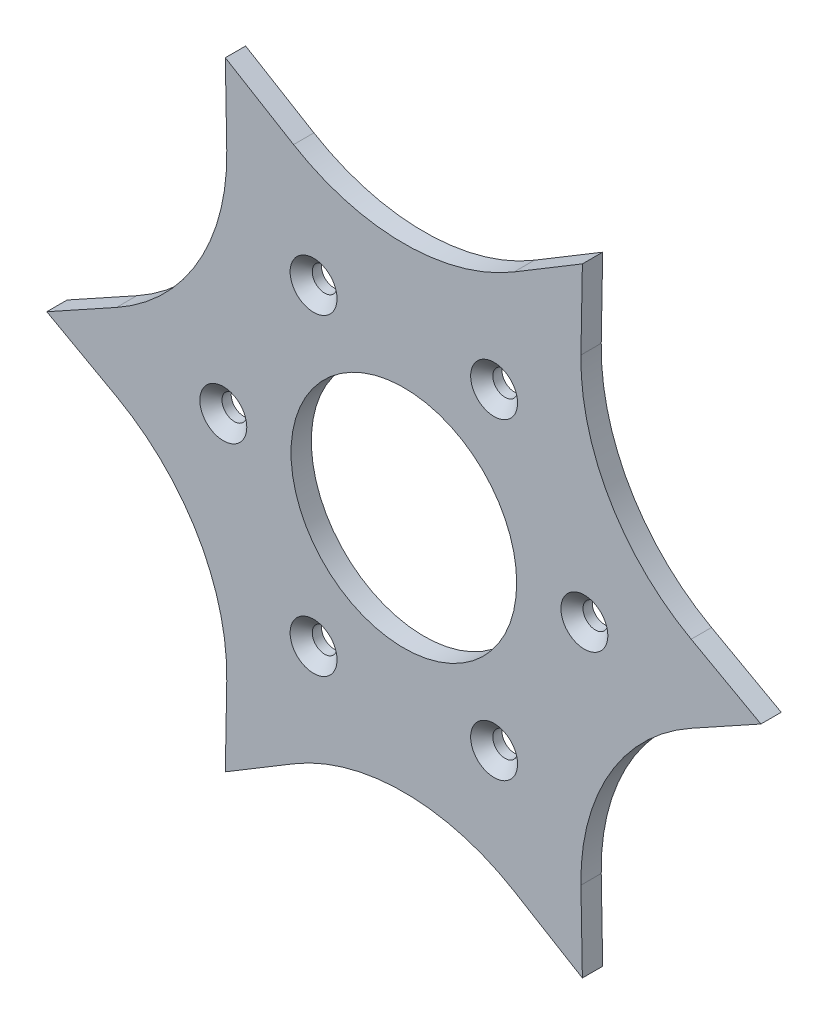
SolidWorks part; units mm, degrees
ref_plane "Front Plane" through (0, 0, 0) normal (0, 0, 1) x (1, 0, 0)
ref_plane "Top Plane" through (0, 0, 0) normal (0, 1, 0) x (1, 0, 0)
ref_plane "Right Plane" through (0, 0, 0) normal (1, 0, 0) x (0, 0, -1)
ref_plane "Plane1" through (0, 0, 62.5456) normal (0, 0, 1) x (1, 0, 0)
sketch "Sketch7" plane through (0, 0, 62.5456) normal (0, 0, 1) x (1, 0, 0)
  line L60 (-39.5574, -68.5154) -> (-24.4318, -59.4109)
  line L63 (39.5574, -68.5154) -> (24.4318, -59.4109)
  line L65 (-39.5574, -68.5154) -> (-39.2354, -50.864)
  line L66 (-79.1148, 0) -> (-63.6672, -8.5469)
  line L69 (-79.1148, 0) -> (-63.6672, 8.5469)
  line L70 (-39.5574, 68.5154) -> (-39.2354, 50.864)
  line L73 (-39.5574, 68.5154) -> (-24.4318, 59.4109)
  line L74 (39.5574, 68.5154) -> (24.4318, 59.4109)
  line L77 (39.5574, 68.5154) -> (39.2354, 50.864)
  line L78 (79.1148, 0) -> (63.6672, 8.5469)
  line L81 (79.1148, 0) -> (63.6672, -8.5469)
  line L82 (39.5574, -68.5154) -> (39.2354, -50.864)
  circle A1 centre (0, 0) radius 25
  circle A19 centre (0, 0) radius 47.9176 construction
  arc A32 (24.4318, -59.4109) -> (-24.4318, -59.4109) centre (0, -100) ccw
  arc A35 (-39.2354, -50.864) -> (-63.6672, -8.5469) centre (-86.6025, -50) ccw
  arc A37 (-63.6672, 8.5469) -> (-39.2354, 50.864) centre (-86.6025, 50) ccw
  arc A39 (-24.4318, 59.4109) -> (24.4318, 59.4109) centre (0, 100) ccw
  arc A41 (39.2354, 50.864) -> (63.6672, 8.5469) centre (86.6025, 50) ccw
  arc A43 (63.6672, -8.5469) -> (39.2354, -50.864) centre (86.6025, -50) ccw
  point P32 (0, 0)
  point P39 (-85.1007, 50.0037)
  point P40 (46.5, 100)
  point P41 (0, 100)
  point P42 (-41.6025, 50)
  point P43 (-40.1025, 50)
  point P45 (-86.6025, 50)
  point P46 (45, 100)
  point P51 (0, 100)
  point P136 (0, 0)
  point P183 (0, 0)
  dimension "D3" = 50
extrude "Boss-Extrude5" add sketch "Sketch7" along normal blind 4.5 separate body
sketch "Sketch8" plane through (0, 0, 67.0456) normal (0, 0, 1) x (1, 0, 0)
  line L0 (0, 0) -> (-119.3408, 0)
hole_wizard "CSK for M5 Flat Head Machine Screw1" positions "Sketch12" profile "Sketch11" countersink size "M5" standard "ANSI Metric" end condition through all
sketch "Sketch12" plane through (0, 0, 67.0456) normal (0, 0, 1) x (1, 0, 0)
  line L0 (0, 0) -> (-119.3408, 0) construction
  point P0 (-40, 0)
  dimension "D1" = 0
  dimension "D2" = 40
sketch "Sketch11" plane through (-40, 0, 67.0456) normal (1, 0, 0) x (0, -1, 0)
  line L0 (0, 0) -> (0, 4.5)
  line L1 (0, 4.5) -> (2.75, 4.5)
  line L2 (2.75, 4.5) -> (2.75, 2.45)
  line L3 (2.75, 2.45) -> (5.2, 0)
  line L5 (5.2, 0) -> (0, 0)
  line L6 (-2.75, 2.45) -> (-5.2, 0) construction
  line L11 (0, -6.35) -> (0, 107.95) construction
  dimension "Thru Hole Dia." = 5.5
  dimension "Thru Hole Depth" = 4.5
  dimension "Near C'Sink Dia." = 10.4
  dimension "Near C'Sink Angle" = 90
pattern_circular "CirPattern1" count 6 over 360 about axis through (0, 0, 0) along (0, 0, 1) of "CSK for M5 Flat Head Machine Screw1"
